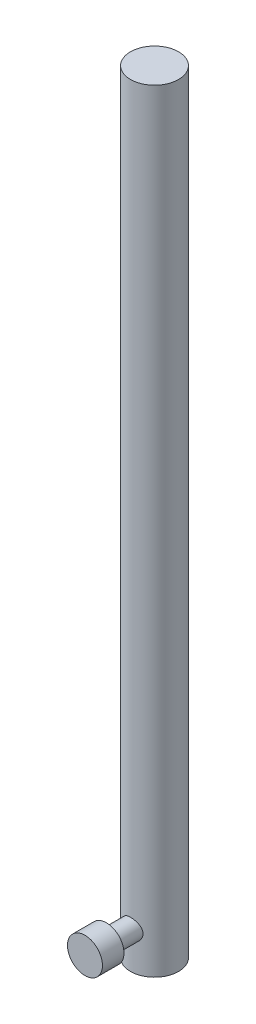
SolidWorks part; units mm, degrees
ref_plane "Front Plane" through (0, 0, 0) normal (0, 0, 1) x (1, 0, 0)
ref_plane "Top Plane" through (0, 0, 0) normal (0, 1, 0) x (1, 0, 0)
ref_plane "Right Plane" through (0, 0, 0) normal (1, 0, 0) x (0, 0, -1)
sketch "Sketch1" plane through (0, 0, 0) normal (0, 1, 0) x (1, 0, 0)
  circle A0 centre (0, 0) radius 3.175
  dimension "D1" = 6.35
extrude "Extrude1" add sketch "Sketch1" along normal blind 102.108
sketch "Sketch2" plane through (0, 0, 0) normal (0, -1, 0) x (1, 0, 0)
  circle A0 centre (0, 0) radius 1
  dimension "D1" = 2
extrude "Extrude2" cut sketch "Sketch2" against normal blind 6.35
sketch "Sketch4" plane through (0, 0, 0) normal (0, 0, 1) x (1, 0, 0)
  line L0 (-3.175, 0) -> (3.175, 0) construction
  circle A0 centre (0, 4.8538) radius 1.3538
  point P2 (0, 3.5)
  dimension "D2" = 2.7076
  dimension "D1" = 3.5
extrude "Boss-Extrude2" add sketch "Sketch4" along normal blind 6.35
sketch "Sketch5" plane through (0, 0, 6.35) normal (0, 0, 1) x (1, 0, 0)
  circle A0 centre (0, 4.8538) radius 2.3114
  dimension "D1" = 4.6228
extrude "Boss-Extrude3" add sketch "Sketch5" along normal blind 2.8448
